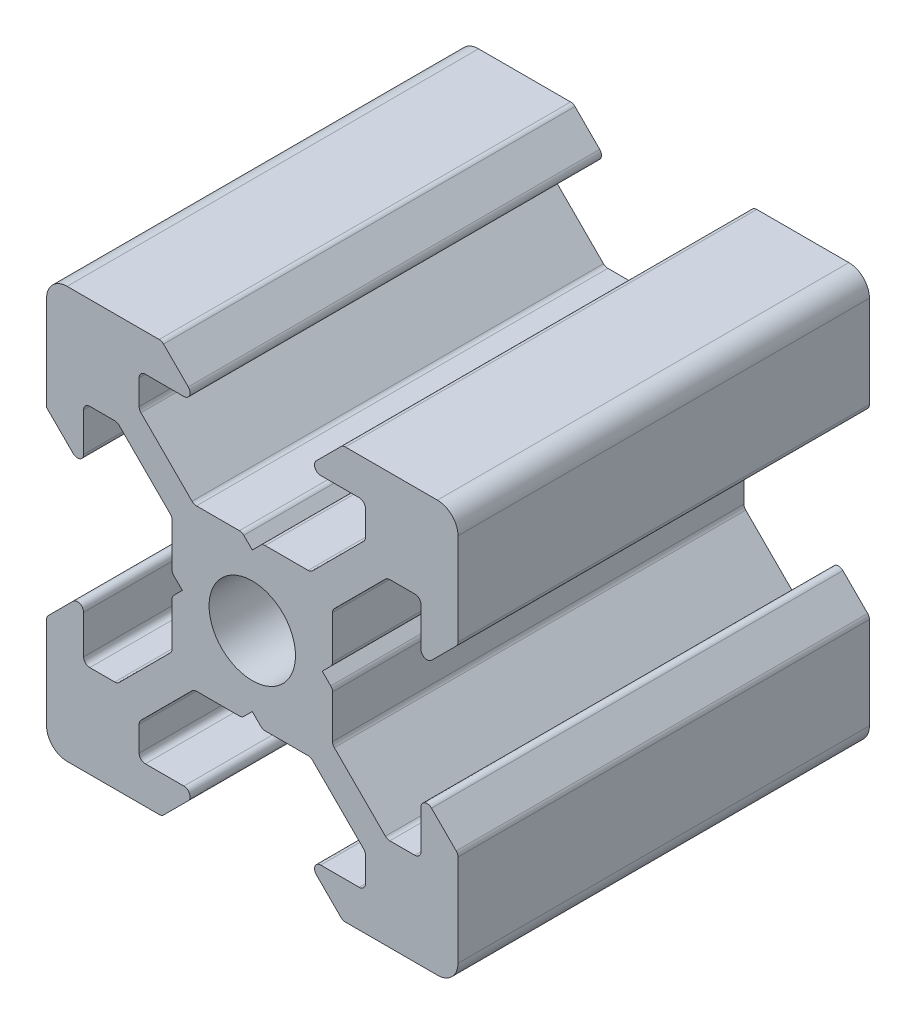
SolidWorks part; units mm, degrees
material "АД31Т ГОСТ 4784-97"
ref_plane "Спереди" through (0, 0, 0) normal (0, 0, 1) x (1, 0, 0)
ref_plane "Сверху" through (0, 0, 0) normal (0, 1, 0) x (1, 0, 0)
ref_plane "Справа" through (0, 0, 0) normal (1, 0, 0) x (0, 0, -1)
sketch "Эскиз1" plane through (0, 0, 0) normal (0, 0, 1) x (1, 0, 0)
  line L0 (0, -12.9654) -> (0, 12.9654) construction
  line L1 (-12.9654, 0) -> (12.9654, 0) construction
  line L2 (0, 0) -> (-18.3359, 18.3359) construction
  line L3 (-10, 10) -> (-4.4, 10)
  line L4 (-4.4, 10) -> (-2.6, 8.2)
  line L5 (-2.6, 8.2) -> (-5.4993, 8.2)
  line L6 (-5.4993, 8.2) -> (-5.4993, 6.56)
  line L7 (-5.4993, 6.56) -> (-2.84, 3.9007)
  line L8 (-2.84, 3.9007) -> (-0.5, 3.9007)
  line L9 (-0.5, 3.9007) -> (0, 3.4007)
  line L10 (-3.9007, 0.5) -> (-3.4007, 0)
  line L11 (-3.9007, 2.84) -> (-3.9007, 0.5)
  line L12 (-6.56, 5.4993) -> (-3.9007, 2.84)
  line L13 (-8.2, 5.4993) -> (-6.56, 5.4993)
  line L14 (-8.2, 2.6) -> (-8.2, 5.4993)
  line L15 (-10, 4.4) -> (-8.2, 2.6)
  line L16 (-10, 10) -> (-10, 4.4)
  line L17 (10, 10) -> (10, 4.4)
  line L18 (10, 4.4) -> (8.2, 2.6)
  line L19 (8.2, 2.6) -> (8.2, 5.4993)
  line L20 (8.2, 5.4993) -> (6.56, 5.4993)
  line L21 (6.56, 5.4993) -> (3.9007, 2.84)
  line L22 (3.9007, 2.84) -> (3.9007, 0.5)
  line L23 (3.9007, 0.5) -> (3.4007, 0)
  line L24 (0.5, 3.9007) -> (0, 3.4007)
  line L25 (2.84, 3.9007) -> (0.5, 3.9007)
  line L26 (5.4993, 6.56) -> (2.84, 3.9007)
  line L27 (5.4993, 8.2) -> (5.4993, 6.56)
  line L28 (2.6, 8.2) -> (5.4993, 8.2)
  line L29 (4.4, 10) -> (2.6, 8.2)
  line L30 (10, 10) -> (4.4, 10)
  line L31 (3.9007, -0.5) -> (3.4007, 0)
  line L32 (-3.9007, -0.5) -> (-3.4007, 0)
  line L33 (10, -10) -> (4.4, -10)
  line L34 (4.4, -10) -> (2.6, -8.2)
  line L35 (2.6, -8.2) -> (5.4993, -8.2)
  line L36 (5.4993, -8.2) -> (5.4993, -6.56)
  line L37 (5.4993, -6.56) -> (2.84, -3.9007)
  line L38 (2.84, -3.9007) -> (0.5, -3.9007)
  line L39 (0.5, -3.9007) -> (0, -3.4007)
  line L40 (3.9007, -2.84) -> (3.9007, -0.5)
  line L41 (6.56, -5.4993) -> (3.9007, -2.84)
  line L42 (8.2, -5.4993) -> (6.56, -5.4993)
  line L43 (8.2, -2.6) -> (8.2, -5.4993)
  line L44 (10, -4.4) -> (8.2, -2.6)
  line L45 (10, -10) -> (10, -4.4)
  line L46 (-10, -10) -> (-10, -4.4)
  line L47 (-10, -4.4) -> (-8.2, -2.6)
  line L48 (-8.2, -2.6) -> (-8.2, -5.4993)
  line L49 (-8.2, -5.4993) -> (-6.56, -5.4993)
  line L50 (-6.56, -5.4993) -> (-3.9007, -2.84)
  line L51 (-3.9007, -2.84) -> (-3.9007, -0.5)
  line L52 (-0.5, -3.9007) -> (0, -3.4007)
  line L53 (-2.84, -3.9007) -> (-0.5, -3.9007)
  line L54 (-5.4993, -6.56) -> (-2.84, -3.9007)
  line L55 (-5.4993, -8.2) -> (-5.4993, -6.56)
  line L56 (-2.6, -8.2) -> (-5.4993, -8.2)
  line L57 (-4.4, -10) -> (-2.6, -8.2)
  line L58 (-10, -10) -> (-4.4, -10)
  circle A0 centre (0, 0) radius 2.1
  dimension "D5" = 2.6
  dimension "D10" = 4.2
  dimension "D2" = 10
  dimension "D3" = 1.64
  dimension "D4" = 1.5
  dimension "D6" = 1.8
  dimension "D7" = 2.84
  dimension "D8" = 0.5
  dimension "D9" = 45
extrude "Бобышка-Вытянуть1" add sketch "Эскиз1" along normal blind 20
fillet "Скругление1" radius 1 4 edges at (-10, -10, 10) (10, -10, 10) (10, 10, 10) (-10, 10, 10)
fillet "Скругление2" radius 0.3 47 edges at (10, 4.4, 10) (8.2, 2.6, 10) (8.2, 5.4993, 10) (6.56, 5.4993, 10) (3.9007, 2.84, 10) (3.9007, 0.5, 10) (3.9007, -0.5, 10) (3.9007, -2.84, 10) (6.56, -5.4993, 10) (10, -4.4, 10) (8.2, -5.4993, 10) (8.2, -2.6, 10) (4.4, -10, 10) (2.6, -8.2, 10) (5.4993, -8.2, 10) (5.4993, -6.56, 10) (2.84, -3.9007, 10) (0.5, -3.9007, 10) (-0.5, -3.9007, 10) (-2.84, -3.9007, 10) (-5.4993, -6.56, 10) (-5.4993, -8.2, 10) (-2.6, -8.2, 10) (-4.4, -10, 10) (-10, -4.4, 10) (-8.2, -2.6, 10) (-8.2, -5.4993, 10) (-6.56, -5.4993, 10) (-3.9007, -2.84, 10) (-3.9007, -0.5, 10) (-3.9007, 0.5, 10) (-3.9007, 2.84, 10) (-6.56, 5.4993, 10) (-8.2, 5.4993, 10) (-8.2, 2.6, 10) (-4.4, 10, 10) (-2.6, 8.2, 10) (-5.4993, 8.2, 10) (-5.4993, 6.56, 10) (-2.84, 3.9007, 10) (-0.5, 3.9007, 10) (0.5, 3.9007, 10) (2.84, 3.9007, 10) (5.4993, 6.56, 10) (5.4993, 8.2, 10) (2.6, 8.2, 10) (4.4, 10, 10)
